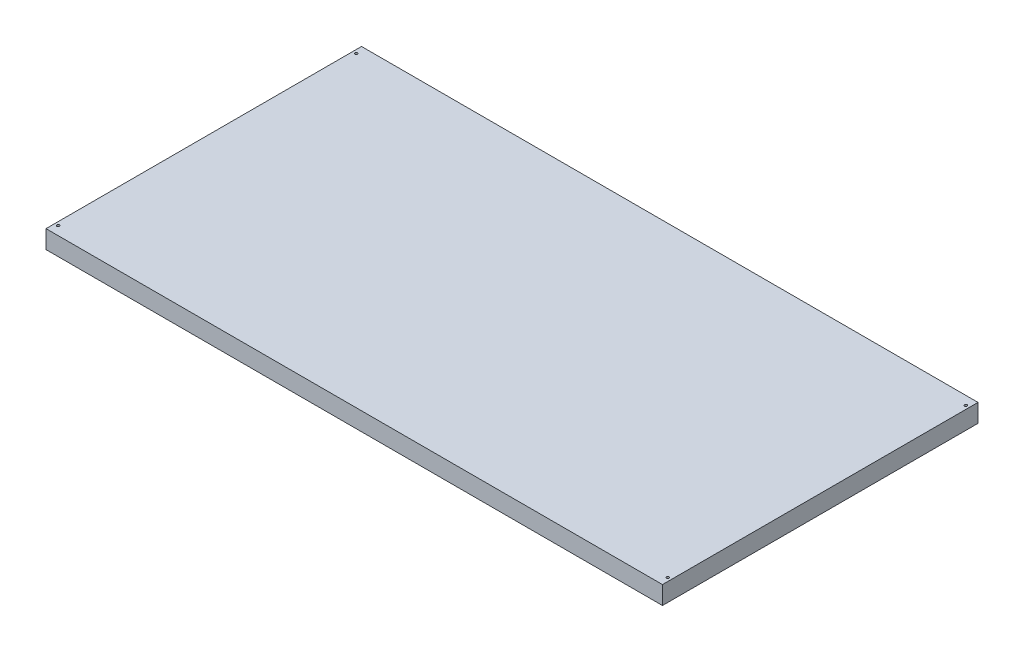
SolidWorks part; units mm, degrees
ref_plane "Front Plane" through (0, 0, 0) normal (0, 0, 1) x (1, 0, 0)
ref_plane "Top Plane" through (0, 0, 0) normal (0, 1, 0) x (1, 0, 0)
ref_plane "Right Plane" through (0, 0, 0) normal (1, 0, 0) x (0, 0, -1)
sketch "Sketch1" plane through (0, 0, 0) normal (0, 1, 0) x (1, 0, 0)
  line L1 (-779.653, 399.034) -> (779.653, 399.034)
  line L2 (-779.653, 399.034) -> (-779.653, -399.034)
  line L3 (-779.653, -399.034) -> (779.653, -399.034)
  line L4 (779.653, 399.034) -> (779.653, -399.034)
  line L5 (-779.653, 399.034) -> (779.653, -399.034) construction
  line L6 (-779.653, -399.034) -> (779.653, 399.034) construction
  point P0 (0, 0)
  dimension "D1" = 1559.306
  dimension "D2" = 798.068
extrude "Boss-Extrude1" add sketch "Sketch1" along normal blind 45.974
sketch "Sketch2" plane through (0, 45.974, 0) normal (0, 1, 0) x (1, 0, 0)
  line L0 (-779.653, 0) -> (779.653, 0) construction
  line L1 (-779.653, 399.034) -> (-779.653, -399.034) construction
  line L2 (779.653, 399.034) -> (-779.653, 399.034) construction
  line L3 (779.653, -399.034) -> (779.653, 399.034) construction
  line L4 (0, 399.034) -> (0, -399.034) construction
  line L5 (-779.653, -399.034) -> (779.653, -399.034) construction
  circle A0 centre (-771.017, 377.063) radius 3.302
  circle A1 centre (771.017, 377.063) radius 3.302
  circle A2 centre (771.017, -377.063) radius 3.302
  circle A3 centre (-771.017, -377.063) radius 3.302
  point P12 (0, 0)
  point P18 (0, 0)
  dimension "D1" = 6.604
  dimension "D2" = 8.636
  dimension "D3" = 21.971
extrude "Cut-Extrude1" cut sketch "Sketch2" against normal through all
